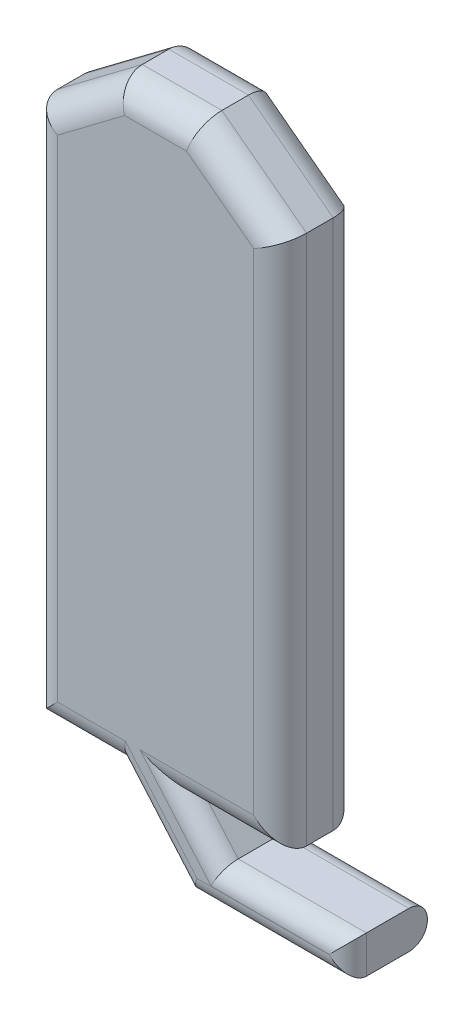
SolidWorks part; units mm, degrees
ref_plane "Front Plane" through (0, 0, 0) normal (0, 0, 1) x (1, 0, 0)
ref_plane "Top Plane" through (0, 0, 0) normal (0, 1, 0) x (1, 0, 0)
ref_plane "Right Plane" through (0, 0, 0) normal (1, 0, 0) x (0, 0, -1)
sketch "Sketch1" plane through (0, 0, 0) normal (0, 0, 1) x (1, 0, 0)
  line L7 (-10.634, 13.2346) -> (-10.634, 18.3146)
  line L8 (-10.634, 18.3146) -> (-9.8226, 18.9261)
  line L9 (-9.8226, 18.9261) -> (-9.0606, 18.9261)
  line L10 (-9.0606, 18.9261) -> (-8.2492, 18.3146)
  line L11 (-8.2492, 18.3146) -> (-8.2492, 13.2346)
  line L20 (-9.1253, 12.5158) -> (-7.6013, 12.5158)
  line L21 (-7.6013, 12.5158) -> (-7.6013, 12.8752)
  line L24 (-10.634, 13.2346) -> (-9.745, 13.2346)
  line L25 (-8.2492, 13.2346) -> (-9.1382, 13.2346)
  line L26 (-9.745, 13.2346) -> (-9.1253, 12.5158)
  line L27 (-9.1382, 13.2346) -> (-8.8283, 12.8752)
  line L28 (-8.8283, 12.8752) -> (-7.6013, 12.8752)
  dimension "D1" = 1.016
  dimension "D2" = 1.016
  dimension "D3" = 0.762
  dimension "D4" = 143
  dimension "D5" = 143
  dimension "D6" = 0.889
  dimension "D7" = 1.524
extrude "Boss-Extrude1" add sketch "Sketch1" along normal blind 0.762
fillet "Fillet6" radius 0.254 14 edges at (-8.6937, 13.2346, 0.762) (-10.1895, 13.2346, 0.762) (-8.6549, 18.6204, 0.762) (-9.4416, 18.9261, 0.762) (-10.2283, 18.6204, 0.762) (-8.2492, 15.7746, 0.762) (-10.634, 15.7746, 0.762) (-8.6549, 18.6204, 0) (-9.4416, 18.9261, 0) (-10.2283, 18.6204, 0) (-10.634, 15.7746, 0) (-10.1895, 13.2346, 0) (-8.6937, 13.2346, 0) (-8.2492, 15.7746, 0)
fillet "Fillet7" radius 0.1778 9 edges at (-8.3633, 12.5158, 0) (-9.5446, 13.0022, 0) (-9.0927, 13.1819, 0) (-8.2148, 12.8752, 0) (-7.6013, 12.6955, 0.762) (-8.3633, 12.5158, 0.762) (-9.5446, 13.0022, 0.762) (-8.2148, 12.8752, 0.762) (-9.0927, 13.1819, 0.762)
